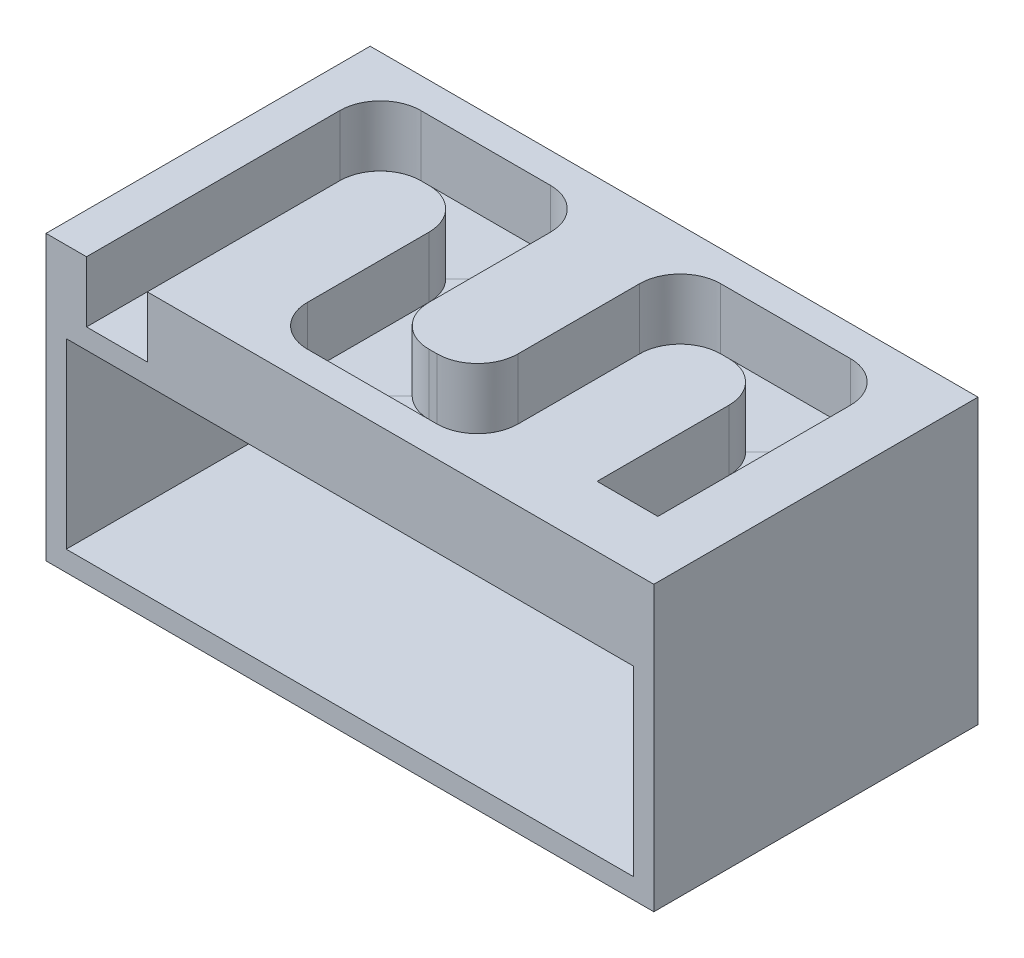
SolidWorks part; units mm, degrees
ref_plane "Front Plane" through (0, 0, 0) normal (0, 0, 1) x (1, 0, 0)
ref_plane "Top Plane" through (0, 0, 0) normal (0, 1, 0) x (1, 0, 0)
ref_plane "Right Plane" through (0, 0, 0) normal (1, 0, 0) x (0, 0, -1)
sketch "Sketch1" plane through (0, 0, 0) normal (0, 1, 0) x (1, 0, 0)
  line L1 (0, 0) -> (150, 0)
  line L2 (0, 0) -> (0, 80)
  line L3 (0, 80) -> (150, 80)
  line L4 (150, 0) -> (150, 80)
  dimension "D1" = 150
  dimension "D2" = 80
extrude "Boss-Extrude1" add sketch "Sketch1" along normal blind 70
shell "Shell1" thickness 5
sketch "Sketch2" plane through (0, 0, 0) normal (0, 0, 1) x (1, 0, 0)
  line L0 (0, 70) -> (150, 70) construction
  line L1 (10, 55) -> (25, 55)
  line L2 (10, 55) -> (10, 70)
  line L3 (10, 70) -> (25, 70)
  line L4 (25, 55) -> (25, 70)
  line L5 (0, 70) -> (0, 0) construction
  dimension "D1" = 15
  dimension "D2" = 15
  dimension "D3" = 10
sketch "Sketch3" plane through (0, 70, 0) normal (0, 1, 0) x (1, 0, 0)
  line L0 (17.5, 0) -> (17.5, 65)
  line L1 (10, 0) -> (25, 0) construction
  line L2 (17.5, 65) -> (54.5, 65)
  line L3 (54.5, 65) -> (54.5, 15)
  line L4 (54.5, 15) -> (91.5, 15)
  line L5 (91.5, 15) -> (91.5, 65)
  line L6 (91.5, 65) -> (128.5, 65)
  line L7 (128.5, 65) -> (128.5, 15)
  line L10 (150, 80) -> (0, 80) construction
  line L11 (54.5, 65) -> (54.5, 80) construction
  line L12 (128.5, 15) -> (128.5, 0) construction
  line L13 (0, 0) -> (150, 0) construction
  point P5 (0, 0)
  point P17 (0, 0)
  dimension "D1" = 37
  dimension "D2" = 15
sweep "Cut-Sweep1" cut profiles "Sketch2" path "Sketch3"
fillet "Fillet1" radius 10 12 edges at (62, 62.5, -22.5) (84, 62.5, -22.5) (84, 62.5, -72.5) (136, 62.5, -72.5) (121, 62.5, -57.5) (99, 62.5, -57.5) (99, 62.5, -7.5) (47, 62.5, -7.5) (47, 62.5, -57.5) (25, 62.5, -57.5) (62, 62.5, -72.5) (10, 62.5, -72.5)
